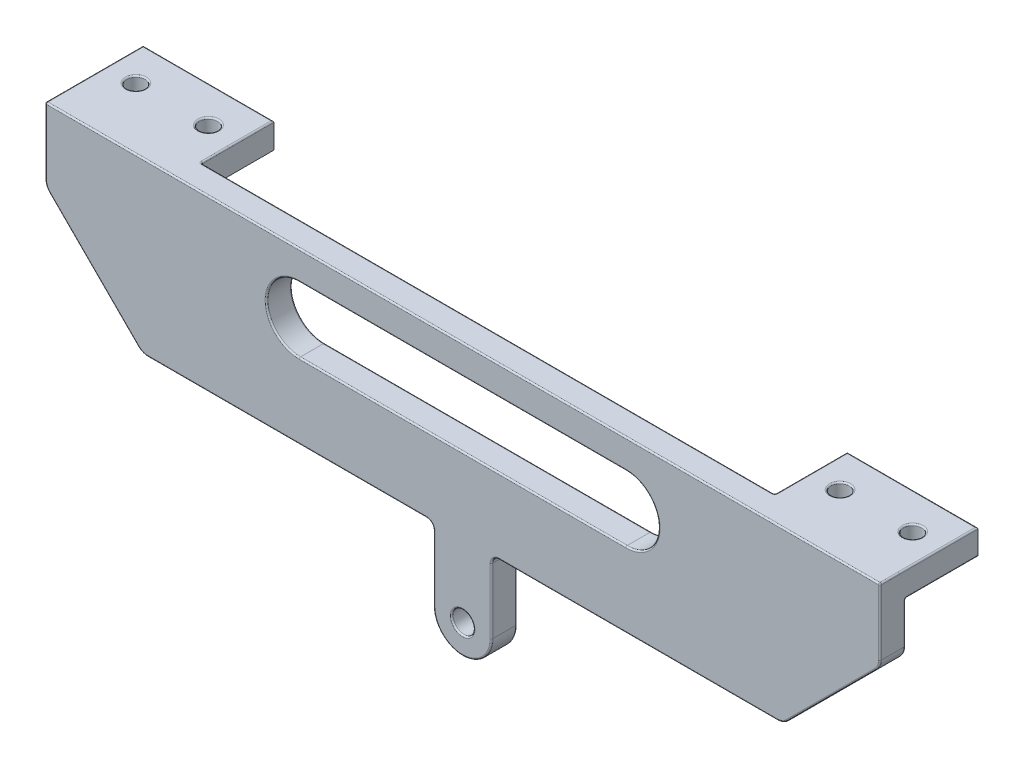
SolidWorks part; units mm, degrees
ref_plane "Front Plane" through (0, 0, 0) normal (0, 0, 1) x (1, 0, 0)
ref_plane "Top Plane" through (0, 0, 0) normal (0, 1, 0) x (1, 0, 0)
ref_plane "Right Plane" through (0, 0, 0) normal (1, 0, 0) x (0, 0, -1)
sketch "Sketch1" plane through (0, 0, 0) normal (0, 0, 1) x (1, 0, 0)
  line L0 (-100, 0) -> (100, 0) construction
  line L1 (-100, 0) -> (0, 100) construction
  line L2 (0, 100) -> (100, 0) construction
  line L3 (0, 100) -> (0, 60) construction
  line L4 (-40, 60) -> (40, 60) construction
  line L5 (0, 0) -> (-50, 50) construction
  circle A0 centre (-100, 0) radius 20
  circle A1 centre (0, 0) radius 20
  circle A2 centre (100, 0) radius 20
  point P4 (0, 0)
  point P9 (0, 60)
  dimension "D1" = 40
  dimension "D2" = 200
  dimension "D3" = 90
  dimension "D4" = 80
  dimension "D5" = 90
sketch "Sketch2" plane through (0, 0, 0) normal (0, 0, 1) x (1, 0, 0)
  line L0 (-56.5165, 43.4835) -> (-40, 60) construction
  line L1 (-100, 0) -> (0, 100) construction
  line L2 (-40, 60) -> (40, 60) construction
  line L3 (40, 60) -> (86.565, 13.435) construction
  line L4 (0, 100) -> (100, 0) construction
  line L5 (-49.4454, 36.4124) -> (-35.8579, 50)
  line L6 (-35.8579, 50) -> (35.8579, 50)
  line L7 (35.8579, 50) -> (79.4939, 6.364)
  line L8 (-63.5876, 50.5546) -> (-44.1421, 70)
  line L9 (-44.1421, 70) -> (44.1421, 70)
  line L10 (44.1421, 70) -> (93.636, 20.5061)
  line L11 (-63.5876, 50.5546) -> (-49.4454, 36.4124)
  line L12 (79.4939, 6.364) -> (93.636, 20.5061)
  line L13 (104.5962, 4.5962) -> (91.1612, 18.0312)
  line L14 (81.9688, 8.8388) -> (95.4038, -4.5962)
  line L15 (75.9584, 9.8995) -> (90.1005, 24.0416) construction
  line L16 (0, 100) -> (0, 60) construction
  line L17 (-3.4532, 85.4203) -> (-6, 70)
  line L18 (0, 84.85) -> (0, 84.8364) construction
  line L19 (3.4532, 85.4203) -> (6, 70)
  circle A0 centre (100, 0) radius 3.5
  circle A1 centre (100, 0) radius 10 construction
  arc A2 (95.4038, -4.5962) -> (104.5962, 4.5962) centre (100, 0) ccw
  circle A3 centre (79.4939, 13.435) radius 1
  circle A4 centre (100, 0) radius 6.5 construction
  circle A5 centre (86.565, 20.5061) radius 1
  circle A6 centre (0, 84.85) radius 1.5
  arc A7 (3.4532, 85.4203) -> (-3.4532, 85.4203) centre (0, 84.85) ccw
  circle A8 centre (0, 60) radius 1.5
  circle A9 centre (-50, 50) radius 1.5
  circle A10 centre (0, 84.85) radius 3.5 construction
  point P28 (106.5, 0)
  point P48 (3.5, 82)
  dimension "D4" = 7
  dimension "D5" = 20
  dimension "D9" = 2
  dimension "D11" = 14.85
  dimension "D12" = 3
  dimension "D14" = 6
  dimension "D15" = 3
  dimension "D1" = 10
  dimension "D3" = 27.5
  dimension "D7" = 19
  dimension "D8" = 5
  dimension "D10" = 5
  dimension "D2" = 10
  dimension "D6" = 3
  dimension "D13" = 2
sketch "Sketch3" plane through (0, 0, 0) normal (0, 0, 1) x (1, 0, 0)
  line L0 (-86.565, 13.435) -> (-50, 50) construction
  line L1 (-100, 0) -> (0, 100) construction
  line L2 (-50, 50) -> (-13.435, 13.435) construction
  line L3 (0, 0) -> (-50, 50) construction
  line L4 (-79.4939, 6.364) -> (-50, 35.8579)
  line L5 (-50, 35.8579) -> (-20.5061, 6.364)
  line L6 (-93.636, 20.5061) -> (-50, 64.1421)
  line L7 (-50, 64.1421) -> (-6.364, 20.5061)
  line L8 (-93.636, 20.5061) -> (-79.4939, 6.364)
  line L9 (-20.5061, 6.364) -> (-6.364, 20.5061)
  line L10 (-104.5962, 4.5962) -> (-91.1612, 18.0312)
  line L11 (-95.4038, -4.5962) -> (-81.9688, 8.8388)
  line L12 (-4.5962, -4.5962) -> (-18.0312, 8.8388)
  line L13 (4.534, 4.6576) -> (-9.0191, 17.8509)
  line L14 (-90.1005, 24.0416) -> (-75.9584, 9.8995) construction
  line L15 (-24.0416, 9.8995) -> (-9.8995, 24.0416) construction
  circle A0 centre (-100, 0) radius 3.5
  circle A1 centre (-100, 0) radius 10 construction
  circle A2 centre (0, 0) radius 3.5
  circle A3 centre (0, 0) radius 10 construction
  arc A4 (-4.5962, -4.5962) -> (4.534, 4.6576) centre (0, 0) ccw
  arc A5 (-104.5962, 4.5962) -> (-95.4038, -4.5962) centre (-100, 0) ccw
  circle A7 centre (0, 0) radius 20 construction
  circle A8 centre (-86.565, 20.5061) radius 1
  circle A9 centre (0, 0) radius 6.5 construction
  circle A10 centre (-79.4939, 13.435) radius 1
  circle A11 centre (-20.5061, 13.435) radius 1
  circle A12 centre (-13.435, 20.5061) radius 1
  circle A13 centre (-50, 50) radius 1.5 construction
  circle A14 centre (-50, 50) radius 1.5
  point P34 (6.5, 0)
  dimension "D1" = 7
  dimension "D2" = 20
  dimension "D4" = 10
  dimension "D10" = 2
  dimension "D6" = 19
  dimension "D7" = 19
  dimension "D8" = 5
  dimension "D9" = 5
  dimension "D11" = 5
  dimension "D12" = 5
  dimension "D3" = 3
  dimension "D5" = 10
sketch "Sketch4" plane through (0, 0, 0) normal (0, 0, 1) x (1, 0, 0)
  line L0 (0, 60) -> (0, 138.097) construction
  line L1 (-57.5, 93.3579) -> (57.5, 93.3579)
  line L2 (57.5, 93.3579) -> (57.5, 83.3579)
  line L3 (57.5, 83.3579) -> (44.1421, 70)
  line L4 (-44.1421, 70) -> (44.1421, 70) construction
  line L5 (44.1421, 70) -> (-44.1421, 70)
  line L6 (44.1421, 70) -> (93.636, 20.5061) construction
  line L7 (4, 60) -> (4, 70)
  line L8 (-4, 60) -> (-4, 70)
  line L9 (-57.5, 83.3579) -> (-44.1421, 70)
  line L10 (-57.5, 93.3579) -> (-57.5, 83.3579)
  line L11 (-22.5, 84.8579) -> (22.5, 84.8579) construction
  line L12 (-22.5, 89.3579) -> (22.5, 89.3579)
  line L13 (-22.5, 80.3579) -> (22.5, 80.3579)
  circle A0 centre (0, 60) radius 1.5 construction
  circle A1 centre (0, 60) radius 1.5
  arc A2 (-4, 60) -> (4, 60) centre (0, 60) ccw
  arc A3 (-22.5, 89.3579) -> (-22.5, 80.3579) centre (-22.5, 84.8579) ccw
  circle A4 centre (0, 60) radius 4 construction
  arc A5 (22.5, 80.3579) -> (22.5, 89.3579) centre (22.5, 84.8579) ccw
  point P23 (4, 60)
  point P25 (0, 70)
  point P27 (0, 93.3579)
  point P29 (0, 84.8579)
  dimension "D1" = 57.5
  dimension "D2" = 10
  dimension "D4" = 45
  dimension "D5" = 9
  dimension "D6" = 4
  dimension "D3" = 2.5
sketch "Sketch5" plane through (0, 0, 0) normal (0, 0, 1) x (1, 0, 0)
  line L0 (4, 60) -> (4, 70) construction
  line L1 (-4, 60) -> (-4, 70) construction
  line L2 (-22.5, 80.3579) -> (22.5, 80.3579)
  line L3 (22.5, 89.3579) -> (-22.5, 89.3579)
  line L4 (-22.5, 80.3579) -> (22.5, 80.3579)
  line L5 (22.5, 89.3579) -> (-22.5, 89.3579)
  line L6 (57.5, 93.3579) -> (-57.5, 93.3579)
  line L7 (57.5, 83.3579) -> (57.5, 93.3579)
  line L8 (44.1421, 70) -> (57.5, 83.3579)
  line L9 (-44.1421, 70) -> (44.1421, 70)
  line L10 (-57.5, 83.3579) -> (-44.1421, 70)
  line L11 (-57.5, 93.3579) -> (-57.5, 83.3579)
  line L12 (57.5, 93.3579) -> (-57.5, 93.3579)
  line L13 (57.5, 83.3579) -> (57.5, 93.3579)
  line L14 (44.1421, 70) -> (57.5, 83.3579)
  line L15 (-44.1421, 70) -> (-4, 70)
  line L16 (-57.5, 83.3579) -> (-44.1421, 70)
  line L17 (-57.5, 93.3579) -> (-57.5, 83.3579)
  line L18 (4, 60) -> (4, 70)
  line L19 (-4, 60) -> (-4, 70)
  line L20 (4, 70) -> (44.1421, 70)
  arc A0 (-4, 60) -> (4, 60) centre (0, 60) ccw construction
  circle A1 centre (0, 60) radius 1.5
  circle A2 centre (0, 60) radius 1.5
  arc A3 (-4, 60) -> (4, 60) centre (0, 60) ccw
  arc A4 (22.5, 80.3579) -> (22.5, 89.3579) centre (22.5, 84.8579) ccw
  arc A5 (-22.5, 89.3579) -> (-22.5, 80.3579) centre (-22.5, 84.8579) ccw
  arc A6 (22.5, 80.3579) -> (22.5, 89.3579) centre (22.5, 84.8579) ccw
  arc A7 (-22.5, 89.3579) -> (-22.5, 80.3579) centre (-22.5, 84.8579) ccw
  dimension "D1" = 0
  dimension "D2" = 0
  dimension "D3" = 0
extrude "Boss-Extrude1" add sketch "Sketch5" along normal blind 3.5
sketch "Sketch6" plane through (0, 93.3579, 0) normal (0, 1, 0) x (1, 0, 0)
  line L0 (0, 0) -> (0, 37.6127) construction
  line L1 (-48.5, 10) -> (-48.5, 5) construction
  line L2 (-57.5, 0) -> (-39.5, 0)
  line L3 (-57.5, 0) -> (-57.5, 10)
  line L4 (-57.5, 10) -> (-39.5, 10)
  line L5 (-39.5, 0) -> (-39.5, 10)
  line L6 (-48.5, 5) -> (-39.5, 5) construction
  line L7 (48.5, 5) -> (39.5, 5) construction
  line L8 (48.5, 10) -> (48.5, 5) construction
  line L9 (39.5, 0) -> (39.5, 10)
  line L10 (57.5, 10) -> (39.5, 10)
  line L11 (57.5, 0) -> (57.5, 10)
  line L12 (57.5, 0) -> (39.5, 0)
  circle A0 centre (-43.5, 5) radius 1.25
  circle A1 centre (-53.5, 5) radius 1.25
  circle A2 centre (53.5, 5) radius 1.25
  circle A3 centre (43.5, 5) radius 1.25
  dimension "D3" = 2.5
  dimension "D1" = 10
  dimension "D2" = 18
  dimension "D4" = 5
extrude "Boss-Extrude2" add sketch "Sketch6" against normal blind 3.5
fillet "Fillet1" radius 2 4 edges at (57.5, 83.3579, 1.75) (44.1421, 70, 1.75) (-44.1421, 70, 1.75) (-57.5, 83.3579, 1.75)
fillet "Fillet2" radius 1 2 edges at (4, 70, 1.75) (-4, 70, 1.75)
fillet "Fillet3" radius 0.2 58 edges at (57.5, 89.8579, -5) (-57.5, 89.8579, -5) (52.25, 93.3579, -5) (44.75, 93.3579, -5) (-44.75, 93.3579, -5) (-52.25, 93.3579, -5) (-57.5, 93.3579, -3.25) (-48.5, 93.3579, -10) (-39.5, 93.3579, -5) (39.5, 93.3579, -5) (48.5, 93.3579, -10) (57.5, 93.3579, -3.25) (-27, 84.8579, 3.5) (0, 80.3579, 3.5) (27, 84.8579, 3.5) (0, 89.3579, 3.5) (1.5, 60, 3.5) (44.0791, 70.1522, 3.5) (24.1569, 70, 3.5) (4.2929, 69.7071, 3.5) (4, 64.5, 3.5) (0, 56, 3.5) (-4, 64.5, 3.5) (-4.2929, 69.7071, 3.5) (-24.1569, 70, 3.5) (-44.0791, 70.1522, 3.5) (-50.8211, 76.6789, 3.5) (-57.3478, 83.4209, 3.5) (-57.5, 88.7721, 3.5) (0, 93.3579, 3.5) (57.5, 88.7721, 3.5) (57.3478, 83.4209, 3.5) (50.8211, 76.6789, 3.5) (0, 80.3579, 0) (-27, 84.8579, 0) (0, 89.3579, 0) (27, 84.8579, 0) (48.5, 89.8579, 0) (39.5, 91.6079, 0) (0, 93.3579, 0) (-39.5, 91.6079, 0) (-48.5, 89.8579, 0) (-57.5, 87.0221, 0) (-57.3478, 83.4209, 0) (-50.8211, 76.6789, 0) (-44.0791, 70.1522, 0) (-24.1569, 70, 0) (-4.2929, 69.7071, 0) (-4, 64.5, 0) (0, 56, 0) (4, 64.5, 0) (4.2929, 69.7071, 0) (24.1569, 70, 0) (44.0791, 70.1522, 0) (50.8211, 76.6789, 0) (57.3478, 83.4209, 0) (57.5, 87.0221, 0) (1.5, 60, 0)
